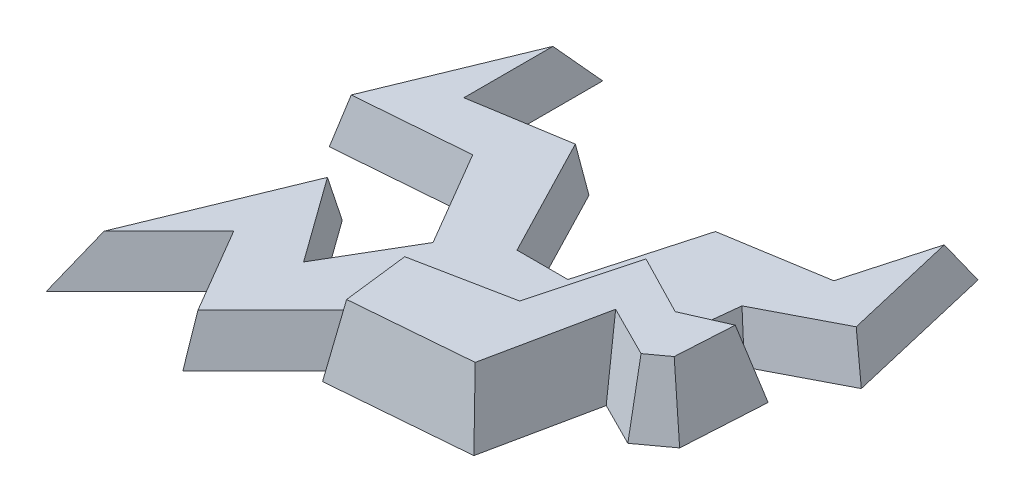
SolidWorks part; units mm, degrees
material "ABS"
ref_plane "Front Plane" through (0, 0, 0) normal (0, 0, 1) x (1, 0, 0)
ref_plane "Top Plane" through (0, 0, 0) normal (0, 1, 0) x (1, 0, 0)
ref_plane "Right Plane" through (0, 0, 0) normal (1, 0, 0) x (0, 0, -1)
sketch "Sketch1" plane through (0, 0, 0) normal (0, 1, 0) x (1, 0, 0)
  line L1 (-17.5, 17.5) -> (17.5, 17.5)
  line L2 (-17.5, 17.5) -> (-17.5, -17.5)
  line L3 (-17.5, -17.5) -> (17.5, -17.5)
  line L4 (17.5, 17.5) -> (17.5, -17.5)
  line L5 (-17.5, 17.5) -> (17.5, -17.5) construction
  line L6 (-17.5, -17.5) -> (17.5, 17.5) construction
  point P0 (0, 0)
  dimension "D1" = 35
sketch "Sketch2" plane through (0, 0, 0) normal (0, 1, 0) x (1, 0, 0)
  line L0 (-6.3864, -1.1108) -> (-0.3878, -0.6158)
  line L1 (-0.3878, -0.6158) -> (0.5914, 4.0854)
  line L2 (0.5914, 4.0854) -> (2.4579, 3.1465)
  line L3 (2.4579, 3.1465) -> (3.742, 4.0854)
  line L4 (3.742, 4.0854) -> (3.9502, 7.6735)
  line L5 (3.9502, 7.6735) -> (1.5991, 6.6419)
  line L6 (1.5991, 6.6419) -> (-1.3485, 8.1604)
  line L7 (-1.3485, 8.1604) -> (-2.5749, 3.568)
  line L8 (-2.5749, 3.568) -> (-6.8476, 2.7179)
  line L9 (-6.8476, 2.7179) -> (-6.3864, -1.1108)
  point P2 (-0.3878, -0.6158)
  point P11 (-6.3864, -1.1108)
  point P12 (-6.3864, 1.52)
  point P13 (0.6423, 4.3298)
  point P14 (2.4579, 3.1465)
  point P15 (3.742, 4.0854)
  point P16 (3.9502, 7.6735)
  point P17 (1.7685, 5.9575)
  point P18 (-2.1321, 6.2717)
  point P19 (-2.7524, 1.8985)
  point P20 (-5.6336, 1.3237)
  point P21 (-3.1848, 2.2411)
  point P22 (1.5991, 6.6419)
  point P23 (-1.3485, 8.1604)
  point P24 (-2.5749, 3.568)
  point P25 (-6.8476, 2.7179)
extrude "Boss-Extrude1" add sketch "Sketch2" along normal blind 3 draft 10
sketch "Sketch3" plane through (0, 0, 0) normal (0, 1, 0) x (1, 0, 0)
  line L0 (-5.4011, 0.6807) -> (-9.7857, -3.704)
  line L1 (-9.7857, -3.704) -> (-11.9561, 0)
  line L2 (-11.9561, 0) -> (-15.6601, -3.704)
  line L3 (-15.6601, -3.704) -> (-11.9561, 5.3052)
  line L4 (-11.9561, 5.3052) -> (-9.2683, 1.5749)
  line L5 (-9.2683, 1.5749) -> (-7.5934, 4.4294)
  line L6 (-7.5934, 4.4294) -> (-9.7857, 8.1709)
  line L7 (-9.7857, 8.1709) -> (-14.968, 7.7617)
  line L8 (-14.968, 7.7617) -> (-11.5498, 16.0757)
  line L9 (-11.5498, 16.0757) -> (-11.5498, 10.886)
  line L10 (-11.5498, 10.886) -> (-7.5934, 11.5299)
  line L11 (-7.5934, 11.5299) -> (-4.885, 6.3001)
  line L12 (-4.885, 6.3001) -> (-3.1839, 6.3001)
  line L13 (-3.1839, 6.3001) -> (-1.8116, 11.208)
  line L14 (-1.8116, 11.208) -> (2.5555, 11.9187)
  line L15 (2.5555, 11.9187) -> (3.9009, 16.7301)
  line L16 (3.9009, 16.7301) -> (5.4342, 10.1897)
  line L17 (5.4342, 10.1897) -> (2.1289, 8.478)
  line L18 (2.1289, 8.478) -> (1.8658, 6.034)
  line L19 (1.8658, 6.034) -> (-0.8654, 5.3937)
  line L20 (-0.8654, 5.3937) -> (-2.4978, 1.4233)
  line L21 (-2.4978, 1.4233) -> (-5.4011, 0.6807)
extrude "Boss-Extrude2" add sketch "Sketch3" along normal blind 2 draft 10
